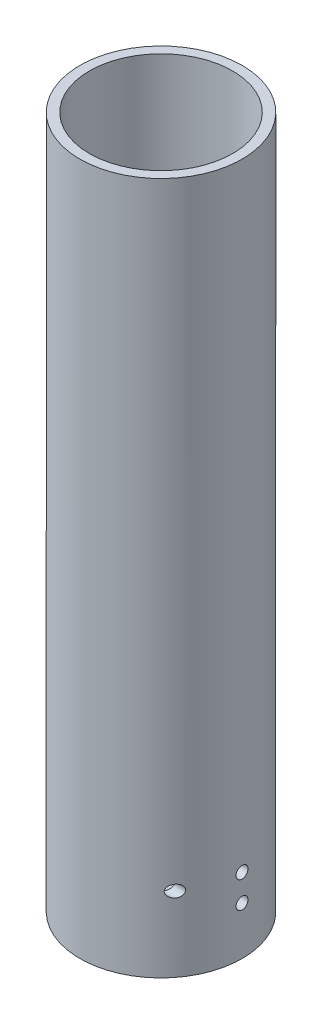
SolidWorks part; units mm, degrees
ref_plane "Front Plane" through (0, 0, 0) normal (0, 0, 1) x (1, 0, 0)
ref_plane "Top Plane" through (0, 0, 0) normal (0, 1, 0) x (1, 0, 0)
ref_plane "Right Plane" through (0, 0, 0) normal (1, 0, 0) x (0, 0, -1)
sketch "Sketch1" plane through (0, 0, 0) normal (0, 1, 0) x (1, 0, 0)
  circle A0 centre (0, 0) radius 17
  circle A1 centre (0, 0) radius 15
  dimension "D1" = 34
  dimension "D2" = 30
extrude "Boss-Extrude1" add sketch "Sketch1" along normal blind 140
sketch "Sketch2" plane through (0, 0, 0) normal (0, -1, 0) x (1, 0, 0)
  circle A0 centre (0, 0) radius 17
extrude "Boss-Extrude2" add sketch "Sketch2" along normal blind 5
sketch "Sketch3" plane through (0, 0, 0) normal (1, 0, 0) x (0, 0, -1)
  circle A0 centre (0, 5.0689) radius 1.25
  circle A1 centre (0, 10.6689) radius 1.25
  circle A2 centre (-10.4296, 10.6689) radius 1.25
  dimension "D1" = 2.5
  dimension "D2" = 2.5
  dimension "D4" = 2.5
  dimension "D3" = 5.6
extrude "Cut-Extrude1" cut sketch "Sketch3" along normal through all
